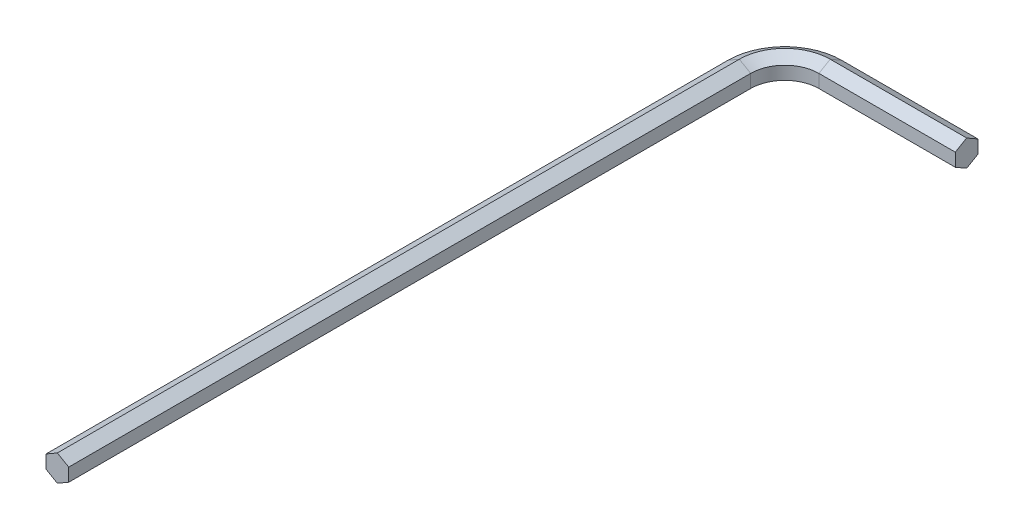
SolidWorks part; units mm, degrees
ref_plane "Front Plane" through (0, 0, 0) normal (0, 0, 1) x (1, 0, 0)
ref_plane "Top Plane" through (0, 0, 0) normal (0, 1, 0) x (1, 0, 0)
ref_plane "Right Plane" through (0, 0, 0) normal (1, 0, 0) x (0, 0, -1)
sketch "Sketch1" plane through (0, 0, 0) normal (0, 0, 1) x (1, 0, 0)
  line L1 (-1.25, 0.7217) -> (-1.25, -0.7217)
  line L2 (-1.25, -0.7217) -> (0, -1.4434)
  line L3 (0, -1.4434) -> (1.25, -0.7217)
  line L4 (1.25, -0.7217) -> (1.25, 0.7217)
  line L5 (1.25, 0.7217) -> (0, 1.4434)
  line L6 (0, 1.4434) -> (-1.25, 0.7217)
  circle A0 centre (0, 0) radius 1.25 construction
  dimension "D1" = 2.5
sketch "Sketch2" plane through (0, 0, 0) normal (0, 1, 0) x (1, 0, 0)
  line L0 (0, 0) -> (0, 75)
  line L1 (5, 80) -> (20, 80)
  arc A0 (0, 75) -> (5, 80) centre (5, 75) cw
  dimension "D3" = 5
  dimension "D1" = 20
  dimension "D2" = 80
sweep "Sweep1" add profiles "Sketch1" path "Sketch2"
